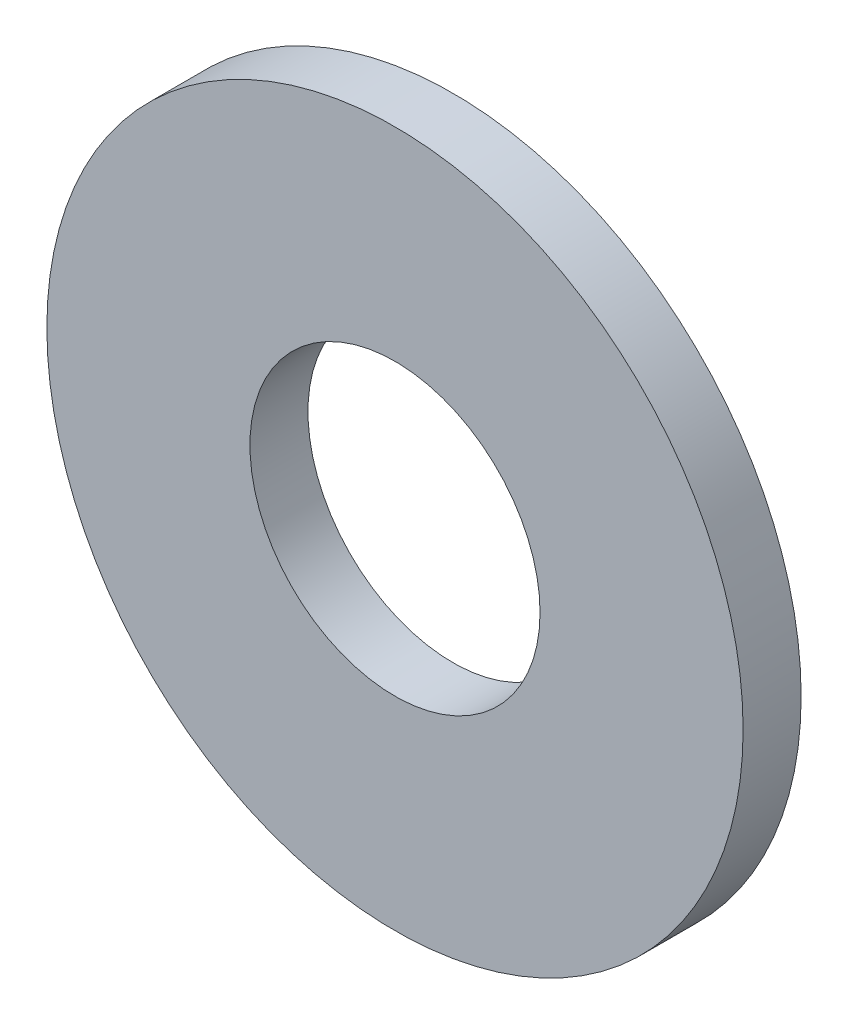
SolidWorks part; units mm, degrees
material "Сталь ШХ15 ГОСТ 801-78"
ref_plane "Plane1" through (0, 0, 0) normal (0, 0, 1) x (1, 0, 0)
ref_plane "Plane2" through (0, 0, 0) normal (0, 1, 0) x (1, 0, 0)
ref_plane "Plane3" through (0, 0, 0) normal (1, 0, 0) x (0, 0, -1)
sketch "Эскиз1" plane through (0, 0, 0) normal (0, 0, 1) x (1, 0, 0)
  circle A0 centre (0, 0) radius 2.5
  circle A1 centre (0, 0) radius 6
  dimension "D1" = 5
  dimension "D2" = 12
extrude "Бобышка-Вытянуть1" add sketch "Эскиз1" along normal blind 1
